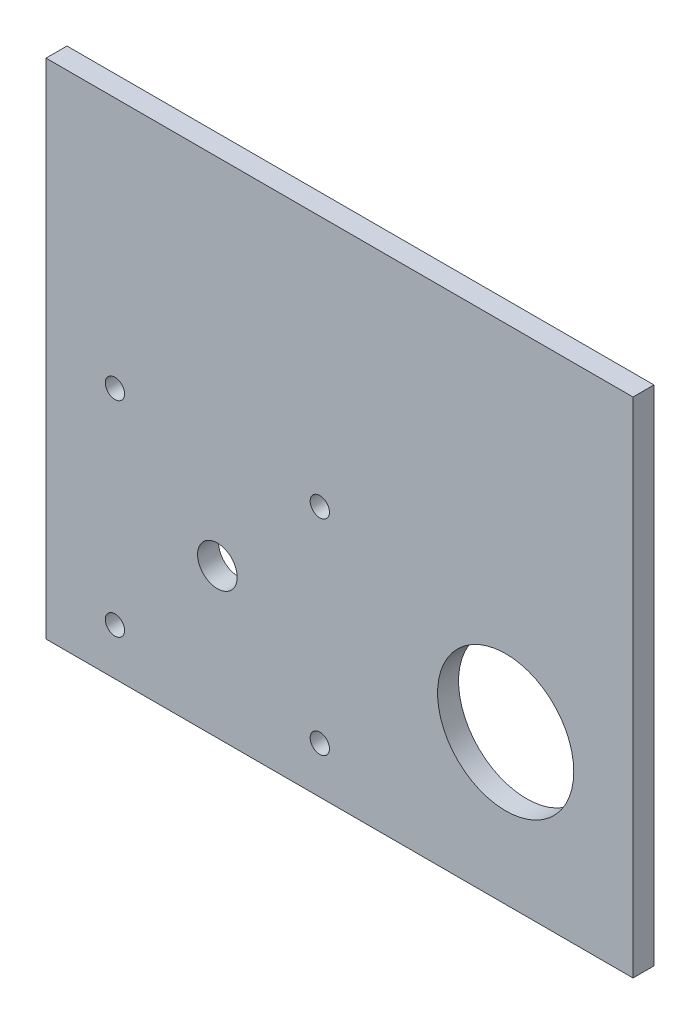
SolidWorks part; units mm, degrees
material "6061 Alloy"
ref_plane "Front Plane" through (0, 0, 0) normal (0, 0, 1) x (1, 0, 0)
ref_plane "Top Plane" through (0, 0, 0) normal (0, 1, 0) x (1, 0, 0)
ref_plane "Right Plane" through (0, 0, 0) normal (1, 0, 0) x (0, 0, -1)
sketch "Sketch1" plane through (0, 0, 0) normal (0, 0, 1) x (1, 0, 0)
  line L0 (10.4352, 38.1) -> (41.4653, 7.07) construction
  line L1 (0, 0) -> (88.9, 0)
  line L2 (0, 0) -> (0, 76.2)
  line L3 (0, 76.2) -> (88.9, 76.2)
  line L4 (88.9, 0) -> (88.9, 76.2)
  line L5 (10.4352, 7.07) -> (41.4653, 7.07) construction
  line L6 (10.4352, 7.07) -> (10.4352, 38.1) construction
  line L7 (10.4352, 38.1) -> (41.4653, 38.1) construction
  line L8 (41.4653, 7.07) -> (41.4653, 38.1) construction
  line L9 (69.6128, 22.585) -> (25.9502, 22.585) construction
  line L10 (79.9252, 22.585) -> (88.9, 22.585) construction
  line L11 (8.9748, 38.1) -> (0, 38.1) construction
  circle A0 centre (10.4352, 38.1) radius 1.4605
  circle A1 centre (41.4653, 38.1) radius 1.4605
  circle A2 centre (41.4653, 7.07) radius 1.4605
  circle A3 centre (10.4352, 7.07) radius 1.4605
  circle A4 centre (25.9502, 22.585) radius 3
  circle A5 centre (69.6128, 22.585) radius 10.3124
  circle A6 centre (25.9502, 22.585) radius 5.5626 construction
  circle A7 centre (69.6128, 22.585) radius 38.1 construction
  point P17 (79.9252, 22.585)
  point P18 (8.9747, 38.1)
  dimension "D3" = 2.921
  dimension "D5" = 6
  dimension "D6" = 20.6248
  dimension "D8" = 11.1252
  dimension "D9" = 76.2
  dimension "D1" = 88.9
  dimension "D2" = 76.2
  dimension "D4" = 31.03
extrude "Boss-Extrude1" add sketch "Sketch1" along normal blind 3.175
sketch "Sketch2" plane through (0, 0, 0) normal (0, 0, -1) x (-1, 0, 0)
  line L0 (-88.9, 76.2) -> (0, 0) construction
  point P4 (-44.45, 38.1)
ref_plane "Center plane" through (44.45, 0, 0) normal (1, 0, 0) x (0, 0, -1)
